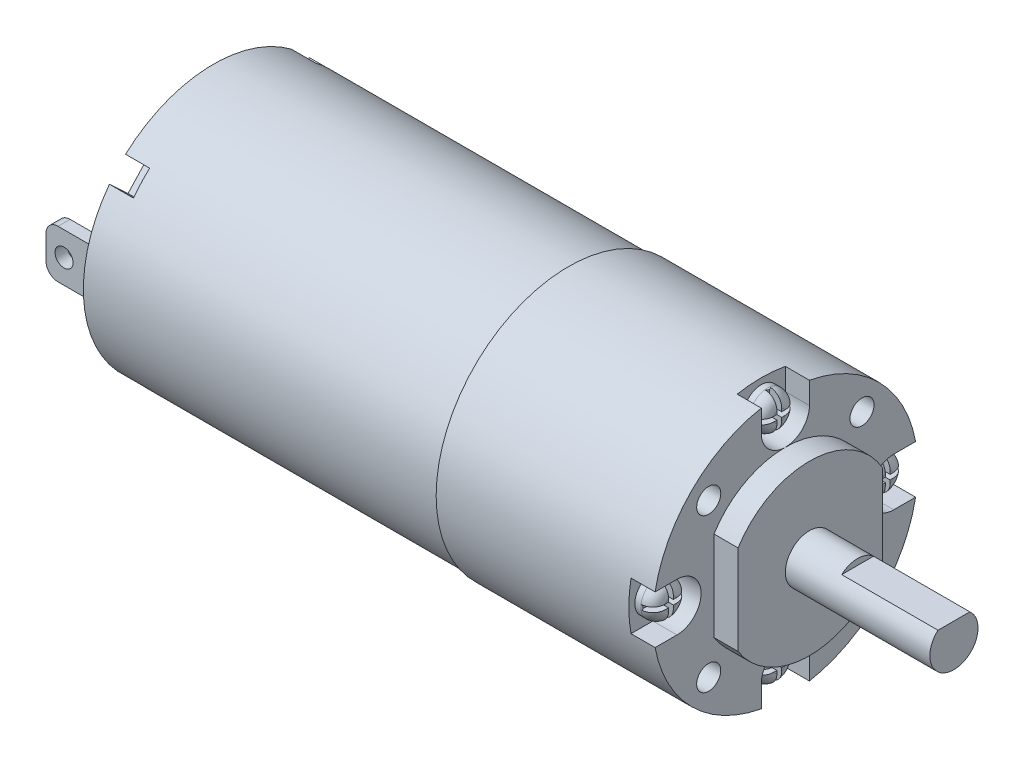
SolidWorks part; units mm, degrees
ref_plane "Plano frontal" through (0, 0, 0) normal (0, 0, 1) x (1, 0, 0)
ref_plane "Plano superior" through (0, 0, 0) normal (0, 1, 0) x (1, 0, 0)
ref_plane "Plano direito" through (0, 0, 0) normal (1, 0, 0) x (0, 0, -1)
sketch "Esboço1" plane through (0, 0, 0) normal (1, 0, 0) x (0, 0, -1)
  line L0 (-1.3229, 1.5) -> (1.3229, 1.5)
  arc A0 (-1.3229, 1.5) -> (1.3229, 1.5) centre (0, 0) ccw
  dimension "D1" = 4
  dimension "D2" = 1.5
extrude "Ressalto-extrusão1" add sketch "Esboço1" along normal blind 8
sketch "Esboço2" plane through (0, 0, 0) normal (-1, 0, 0) x (0, 0, 1)
  circle A0 centre (0, 0) radius 2
  arc A2 (-1.3229, 1.5) -> (1.3229, 1.5) centre (0, 0) ccw construction
extrude "Ressalto-extrusão2" add sketch "Esboço2" along normal blind 4
sketch "Esboço3" plane through (-4, 0, 0) normal (-1, 0, 0) x (0, 0, 1)
  line L0 (5.9273, 3.7239) -> (5.9273, -3.7239)
  line L1 (-6.0727, 3.4817) -> (-6.0727, -3.4817)
  arc A0 (5.9273, 3.7239) -> (-6.0727, 3.4817) centre (0, 0) ccw
  arc A1 (-6.0727, -3.4817) -> (5.9273, -3.7239) centre (0, 0) ccw
  dimension "D1" = 14
  dimension "D2" = 12
  dimension "D3" = 7.4477
extrude "Ressalto-extrusão3" add sketch "Esboço3" along normal blind 2
sketch "Esboço4" plane through (-6, 0, 0) normal (-1, 0, 0) x (0, 0, 1)
  circle A0 centre (0, 0) radius 11
  dimension "D1" = 22
extrude "Ressalto-extrusão4" add sketch "Esboço4" along normal blind 18
sketch "Esboço6" plane through (-24, 0, 0) normal (-1, 0, 0) x (0, 0, 1)
  circle A0 centre (0, 0) radius 10.8
  dimension "D1" = 21.6
extrude "Ressalto-extrusão5" add sketch "Esboço6" along normal blind 29.5
sketch "Esboço7" plane through (-53.5, 0, 0) normal (-1, 0, 0) x (0, 0, 1)
  line L1 (-9.9986, 2.6918) -> (-8.9986, 2.6918)
  line L2 (-9.9986, 2.6918) -> (-9.9986, -1.3082)
  line L3 (-9.9986, -1.3082) -> (-8.9986, -1.3082)
  line L4 (-8.9986, 2.6918) -> (-8.9986, -1.3082)
  line L5 (9.0014, 2.6918) -> (10.0014, 2.6918)
  line L6 (9.0014, 2.6918) -> (9.0014, -1.3082)
  line L7 (9.0014, -1.3082) -> (10.0014, -1.3082)
  line L8 (10.0014, 2.6918) -> (10.0014, -1.3082)
  dimension "D1" = 4
  dimension "D2" = 1
  dimension "D3" = 4
  dimension "D4" = 1
  dimension "D5" = 18
  dimension "D6" = 8.9986
extrude "Ressalto-extrusão6" add sketch "Esboço7" along normal blind 3.9
fillet "Filete1" radius 1 4 edges at (-57.4, -1.3082, 9.5014) (-57.4, 2.6918, 9.5014) (-57.4, -1.3082, -9.4986) (-57.4, 2.6918, -9.4986)
sketch "Esboço8" plane through (0, 0, 10.0014) normal (0, 0, 1) x (1, 0, 0)
  line L0 (-57.4, -0.3082) -> (-57.4, 1.6918) construction
  line L1 (-56.4, 2.6918) -> (-53.5, 2.6918) construction
  circle A0 centre (-55.9, 0.6918) radius 0.75
  dimension "D1" = 1.5
  dimension "D2" = 1.5
  dimension "D3" = 2
extrude "Corte-extrusão1" cut sketch "Esboço8" against normal up to surface and the other way through all
sketch "Esboço9" plane through (-6, 0, 0) normal (1, 0, 0) x (0, 0, -1)
  line L0 (-2, 9) -> (-2, 10.8167)
  line L1 (2, 9) -> (2, 10.8167)
  line L2 (9, 2) -> (10.8167, 2)
  line L3 (9, -2) -> (10.8167, -2)
  line L4 (2, -9) -> (2, -10.8167)
  line L5 (-2, -9) -> (-2, -10.8167)
  line L6 (-9, -2) -> (-10.8167, -2)
  line L7 (-9, 2) -> (-10.8167, 2)
  arc A0 (-2, 9) -> (2, 9) centre (0, 9) ccw
  circle A1 centre (0, 0) radius 11 construction
  arc A2 (-2, 10.8167) -> (2, 10.8167) centre (0, 0) cw
  arc A3 (9, 2) -> (9, -2) centre (9, 0) ccw
  arc A4 (10.8167, 2) -> (10.8167, -2) centre (0, 0) cw
  arc A5 (2, -9) -> (-2, -9) centre (0, -9) ccw
  arc A6 (2, -10.8167) -> (-2, -10.8167) centre (0, 0) cw
  arc A7 (-9, -2) -> (-9, 2) centre (-9, 0) ccw
  arc A8 (-10.8167, -2) -> (-10.8167, 2) centre (0, 0) cw
  point P27 (0, 0)
  dimension "D1" = 4
  dimension "D3" = 11
  dimension "D4" = 2
  dimension "D2" = 9
  dimension "D5" = 1.8167
  dimension "D6" = 4
extrude "Corte-extrusão2" cut sketch "Esboço9" against normal blind 2
sketch "Esboço10" plane through (-6, 0, 0) normal (1, 0, 0) x (0, 0, -1)
  circle A1 centre (-6.3629, 6.365) radius 1
  circle A6 centre (6.365, 6.3629) radius 1
  circle A8 centre (6.3629, -6.365) radius 1
  circle A10 centre (-6.365, -6.3629) radius 1
  point P16 (0, 0)
  point P17 (0, 0)
  dimension "D1" = 6.365
  dimension "D3" = 2
  dimension "D2" = 4
extrude "Corte-extrusão3" cut sketch "Esboço10" against normal blind 2
sketch "Esboço12" plane through (-53.5, 0, 0) normal (-1, 0, 0) x (0, 0, 1)
  line L1 (-6.5076, 5.7282) -> (-5.0449, 7.0922)
  line L4 (-6.5076, 5.7282) -> (-8.5536, 7.9223)
  line L5 (-8.5536, 7.9223) -> (-7.0909, 9.2863)
  line L6 (-7.0909, 9.2863) -> (-5.0449, 7.0922)
  line L7 (9.2863, 7.0909) -> (7.0922, 5.0449)
  line L8 (5.7282, 6.5076) -> (7.0922, 5.0449)
  line L9 (5.7282, 6.5076) -> (7.9223, 8.5536)
  line L10 (7.9223, 8.5536) -> (9.2863, 7.0909)
  line L11 (7.0909, -9.2863) -> (5.0449, -7.0922)
  line L12 (6.5076, -5.7282) -> (5.0449, -7.0922)
  line L13 (6.5076, -5.7282) -> (8.5536, -7.9223)
  line L14 (8.5536, -7.9223) -> (7.0909, -9.2863)
  line L15 (-9.2863, -7.0909) -> (-7.0922, -5.0449)
  line L16 (-5.7282, -6.5076) -> (-7.0922, -5.0449)
  line L17 (-5.7282, -6.5076) -> (-7.9223, -8.5536)
  line L18 (-7.9223, -8.5536) -> (-9.2863, -7.0909)
  point P19 (0, 0)
  dimension "D1" = 3
  dimension "D2" = 2
extrude "Corte-extrusão5" cut sketch "Esboço12" against normal blind 2
sketch "Esboço13" plane through (-8, 0, 0) normal (1, 0, 0) x (0, 0, -1)
  circle A0 centre (-9, 0) radius 1.5
  circle A1 centre (0, 9) radius 1.5
  circle A2 centre (9, 0) radius 1.5
  circle A3 centre (0, -9) radius 1.5
  point P12 (0, 0)
  dimension "D1" = 3
extrude "Ressalto-extrusão7" add sketch "Esboço13" along normal blind 1.5
fillet "Filete2" radius 1 4 edges at (-6.5, 0, 7.5) (-6.5, -9, -1.5) (-6.5, 0, -10.5) (-6.5, 9, -1.5)
sketch "Esboço14" plane through (-6.5, 0, 0) normal (1, 0, 0) x (0, 0, -1)
  line L0 (-9.2, 1.4866) -> (-9.2, 0.2)
  line L1 (-9.2, 0.2) -> (-10.4866, 0.2)
  line L2 (-10.4866, 0.2) -> (-10.4866, -0.2)
  line L3 (-10.4866, -0.2) -> (-9.2, -0.2)
  line L4 (-9.2, -0.2) -> (-9.2, -1.4866)
  line L5 (-9.2, -1.4866) -> (-8.8, -1.4866)
  line L6 (-8.8, -1.4866) -> (-8.8, -0.2)
  line L7 (-8.8, -0.2) -> (-7.5134, -0.2)
  line L8 (-7.5134, -0.2) -> (-7.5134, 0.2)
  line L9 (-7.5134, 0.2) -> (-8.8, 0.2)
  line L10 (-8.8, 0.2) -> (-8.8, 1.4866)
  line L11 (-8.8, 1.4866) -> (-9.2, 1.4866)
  line L12 (-0.2, 10.4866) -> (-0.2, 9.2)
  line L13 (0.2, 9.2) -> (0.2, 10.4866)
  line L14 (0.2, 10.4866) -> (-0.2, 10.4866)
  line L15 (-1.4866, 9.2) -> (-1.4866, 8.8)
  line L16 (-0.2, 9.2) -> (-1.4866, 9.2)
  line L17 (-1.4866, 8.8) -> (-0.2, 8.8)
  line L18 (-0.2, 8.8) -> (-0.2, 7.5134)
  line L19 (0.2, 7.5134) -> (0.2, 8.8)
  line L20 (-0.2, 7.5134) -> (0.2, 7.5134)
  line L21 (0.2, 8.8) -> (1.4866, 8.8)
  line L22 (1.4866, 9.2) -> (0.2, 9.2)
  line L23 (1.4866, 8.8) -> (1.4866, 9.2)
  line L24 (10.4866, 0.2) -> (9.2, 0.2)
  line L25 (9.2, -0.2) -> (10.4866, -0.2)
  line L26 (10.4866, -0.2) -> (10.4866, 0.2)
  line L27 (9.2, 1.4866) -> (8.8, 1.4866)
  line L28 (9.2, 0.2) -> (9.2, 1.4866)
  line L29 (8.8, 1.4866) -> (8.8, 0.2)
  line L30 (8.8, 0.2) -> (7.5134, 0.2)
  line L31 (7.5134, -0.2) -> (8.8, -0.2)
  line L32 (7.5134, 0.2) -> (7.5134, -0.2)
  line L33 (8.8, -0.2) -> (8.8, -1.4866)
  line L34 (9.2, -1.4866) -> (9.2, -0.2)
  line L35 (8.8, -1.4866) -> (9.2, -1.4866)
  line L36 (0.2, -10.4866) -> (0.2, -9.2)
  line L37 (-0.2, -9.2) -> (-0.2, -10.4866)
  line L38 (-0.2, -10.4866) -> (0.2, -10.4866)
  line L39 (1.4866, -9.2) -> (1.4866, -8.8)
  line L40 (0.2, -9.2) -> (1.4866, -9.2)
  line L41 (1.4866, -8.8) -> (0.2, -8.8)
  line L42 (0.2, -8.8) -> (0.2, -7.5134)
  line L43 (-0.2, -7.5134) -> (-0.2, -8.8)
  line L44 (0.2, -7.5134) -> (-0.2, -7.5134)
  line L45 (-0.2, -8.8) -> (-1.4866, -8.8)
  line L46 (-1.4866, -9.2) -> (-0.2, -9.2)
  line L47 (-1.4866, -8.8) -> (-1.4866, -9.2)
  circle A0 centre (-9, 0) radius 1.5 construction
  point P53 (-0.05, 0)
  point P54 (0, 0)
  dimension "D1" = 0.4
  dimension "D2" = 0.4
extrude "Corte-extrusão6" cut sketch "Esboço14" against normal blind 1
